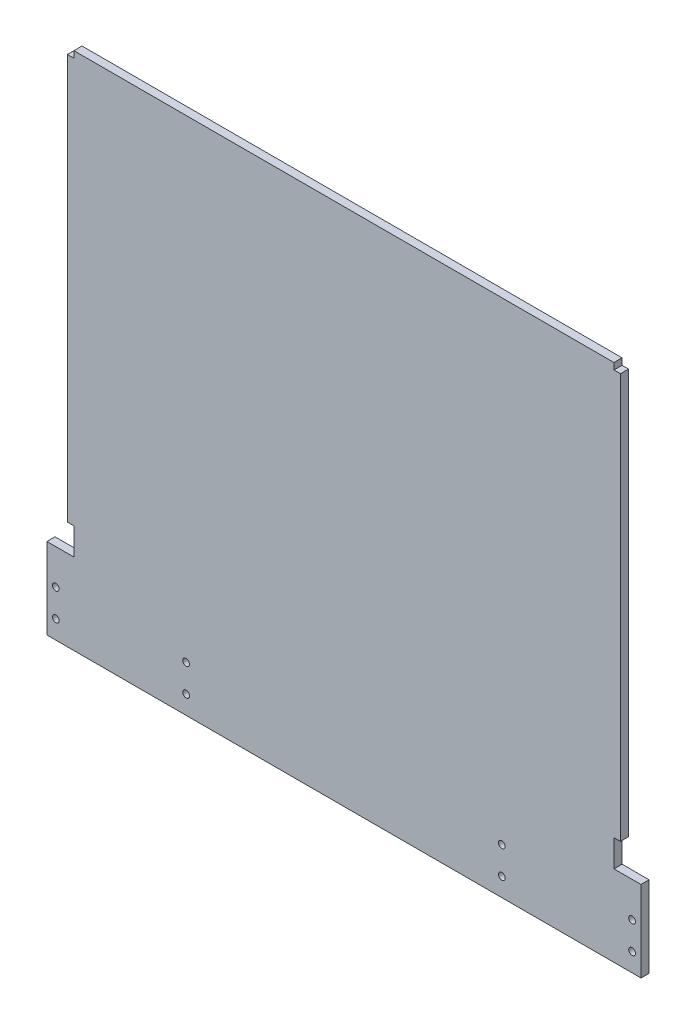
SolidWorks part; units mm, degrees
ref_plane "Plan de face" through (0, 0, 0) normal (0, 0, 1) x (1, 0, 0)
ref_plane "Plan de dessus" through (0, 0, 0) normal (0, 1, 0) x (1, 0, 0)
ref_plane "Plan de droite" through (0, 0, 0) normal (1, 0, 0) x (0, 0, -1)
sketch "Esquisse1" plane through (0, 0, 0) normal (0, 0, 1) x (1, 0, 0)
  line L0 (53.6095, 141.3669) -> (53.6095, -51.0331) construction
  line L1 (-56.3905, -21.0331) -> (-56.3905, -51.0331)
  line L2 (-46.3905, -21.0331) -> (-56.3905, -21.0331)
  line L3 (153.6095, 141.3669) -> (153.6095, 138.9669)
  line L4 (153.6095, 138.9669) -> (156.0095, 138.9669)
  line L5 (156.0095, 138.9669) -> (156.0095, -11.0331)
  line L6 (156.0095, -11.0331) -> (153.6095, -11.0331)
  line L7 (153.6095, -11.0331) -> (153.6095, -21.0331)
  line L8 (153.6095, -21.0331) -> (163.6095, -21.0331)
  line L9 (163.6095, -21.0331) -> (163.6095, -51.0331)
  line L10 (163.6095, -51.0331) -> (-56.3905, -51.0331)
  line L11 (-46.3905, -11.0331) -> (-46.3905, -21.0331)
  line L12 (-48.7905, -11.0331) -> (-46.3905, -11.0331)
  line L13 (-48.7905, 138.9669) -> (-48.7905, -11.0331)
  line L14 (-46.3905, 138.9669) -> (-48.7905, 138.9669)
  line L15 (-46.3905, 141.3669) -> (-46.3905, 138.9669)
  line L16 (-46.3905, 141.3669) -> (153.6095, 141.3669)
  dimension "D2" = 150
  dimension "D3" = 30
  dimension "D4" = 200
  dimension "D5" = 2.4
  dimension "D6" = 2.4
  dimension "D10" = 10
  dimension "D13" = 10
extrude "Boss.-Extru.1" add sketch "Esquisse1" along normal blind 3
sketch "Esquisse2" plane through (0, 0, 3) normal (0, 0, 1) x (1, 0, 0)
  line L2 (163.6095, -51.0331) -> (163.6095, -21.0331) construction
  line L7 (163.6095, -21.0331) -> (153.6095, -21.0331) construction
  line L8 (53.6095, 141.3669) -> (53.6095, -51.0331) construction
  line L10 (153.6095, 141.3669) -> (-46.3905, 141.3669) construction
  line L11 (-56.3905, -51.0331) -> (163.6095, -51.0331) construction
  circle A0 centre (160.3195, -34.0331) radius 1.25
  circle A1 centre (112.0595, -34.0331) radius 1.25
  circle A2 centre (160.3195, -44.1931) radius 1.25
  circle A3 centre (112.0595, -44.1931) radius 1.25
  circle A4 centre (-4.8405, -44.1931) radius 1.25
  circle A5 centre (-53.1005, -44.1931) radius 1.25
  circle A6 centre (-4.8405, -34.0331) radius 1.25
  circle A7 centre (-53.1005, -34.0331) radius 1.25
  dimension "D1" = 2
  dimension "D7" = 2.5
  dimension "D2" = 3.29
  dimension "D3" = 13
  dimension "D6" = 2
  dimension "D4" = 48.26
  dimension "D5" = 2
extrude "Enlèv. mat.-Extru.1" cut sketch "Esquisse2" against normal blind 10
